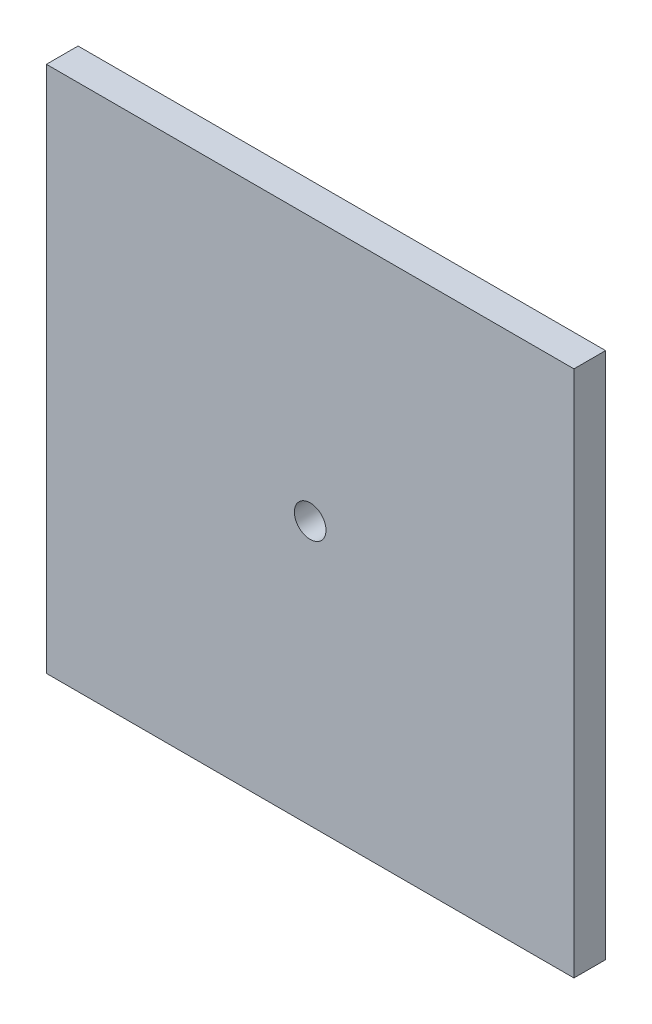
SolidWorks part; units mm, degrees
material "Acrylic (Medium-high impact)"
ref_plane "Front Plane" through (0, 0, 0) normal (0, 0, 1) x (1, 0, 0)
ref_plane "Top Plane" through (0, 0, 0) normal (0, 1, 0) x (1, 0, 0)
ref_plane "Right Plane" through (0, 0, 0) normal (1, 0, 0) x (0, 0, -1)
sketch "Sketch1" plane through (0, 0, 0) normal (0, 0, 1) x (1, 0, 0)
  line L1 (-25, 25) -> (25, 25)
  line L2 (-25, 25) -> (-25, -25)
  line L3 (-25, -25) -> (25, -25)
  line L4 (25, 25) -> (25, -25)
  line L5 (-25, 25) -> (25, -25) construction
  line L6 (-25, -25) -> (25, 25) construction
  point P0 (0, 0)
  dimension "D1" = 50
  dimension "D2" = 50
extrude "Boss-Extrude1" add sketch "Sketch1" along normal blind 3
sketch "Sketch2" plane through (0, 0, 3) normal (0, 0, 1) x (1, 0, 0)
  circle A0 centre (0, 0) radius 1.5
  dimension "D1" = 3
extrude "Cut-Extrude1" cut sketch "Sketch2" against normal through all both and the other way through all
